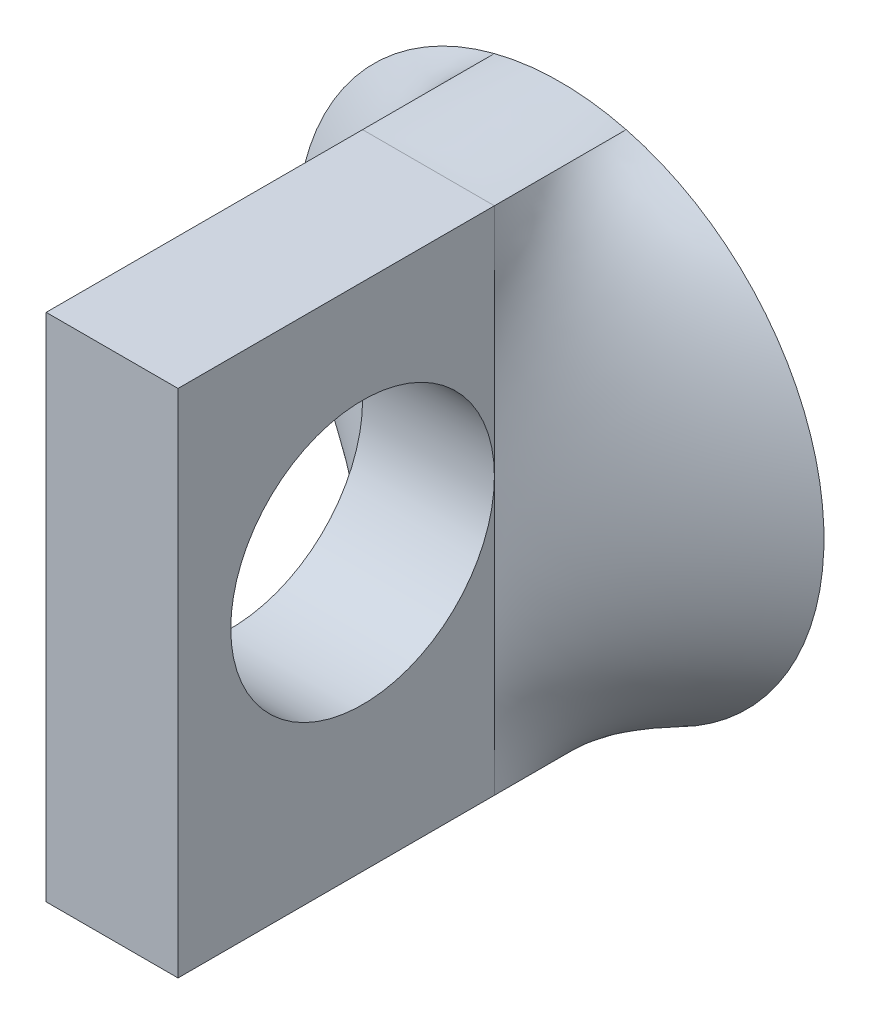
SolidWorks part; units mm, degrees
ref_plane "Front" through (0, 0, 0) normal (0, 0, 1) x (1, 0, 0)
ref_plane "Top" through (0, 0, 0) normal (0, 1, 0) x (1, 0, 0)
ref_plane "Right" through (0, 0, 0) normal (1, 0, 0) x (0, 0, -1)
sketch "Sketch1" plane through (0, 0, 0) normal (0, 0, 1) x (1, 0, 0)
  circle A0 centre (0, 0) radius 12.7
  dimension "D1" = 25.4
ref_plane "Plane1" through (0, 0, 6.35) normal (0, 0, 1) x (1, 0, 0)
sketch "Sketch2" plane through (0, 0, 6.35) normal (0, 0, 1) x (1, 0, 0)
  line L1 (-3.175, 12.2967) -> (3.175, 12.2967)
  line L2 (-3.175, 12.2967) -> (-3.175, -12.2967)
  line L3 (-3.175, -12.2967) -> (3.175, -12.2967)
  line L4 (3.175, 12.2967) -> (3.175, -12.2967)
  line L5 (-3.175, 12.2967) -> (3.175, -12.2967) construction
  line L6 (-3.175, -12.2967) -> (3.175, 12.2967) construction
  circle A0 centre (0, 0) radius 12.7 construction
  point P0 (0, 0)
  dimension "D1" = 6.35
loft "Loft1" add profiles "Sketch2", "Sketch1"
sketch "Sketch3" plane through (0, 0, 6.35) normal (0, 0, 1) x (1, 0, 0)
  line L4 (3.175, -12.2967) -> (3.175, 12.2967)
  line L5 (3.175, 12.2967) -> (-3.175, 12.2967)
  line L6 (-3.175, 12.2967) -> (-3.175, -12.2967)
  line L7 (-3.175, -12.2967) -> (3.175, -12.2967)
  line L8 (3.175, -12.2967) -> (3.175, 12.2967)
  line L9 (3.175, 12.2967) -> (-3.175, 12.2967)
  line L10 (-3.175, 12.2967) -> (-3.175, -12.2967)
  line L11 (-3.175, -12.2967) -> (3.175, -12.2967)
  dimension "D1" = 0
extrude "Boss-Extrude1" add sketch "Sketch3" along normal blind 15.24
sketch "Sketch4" plane through (3.175, 0, 0) normal (1, 0, 0) x (0, 0, -1)
  circle A0 centre (-12.7, 1.0104) radius 6.35
  dimension "D2" = 12.7
  dimension "D1" = 12.7
extrude "Cut-Extrude1" cut sketch "Sketch4" against normal through all
